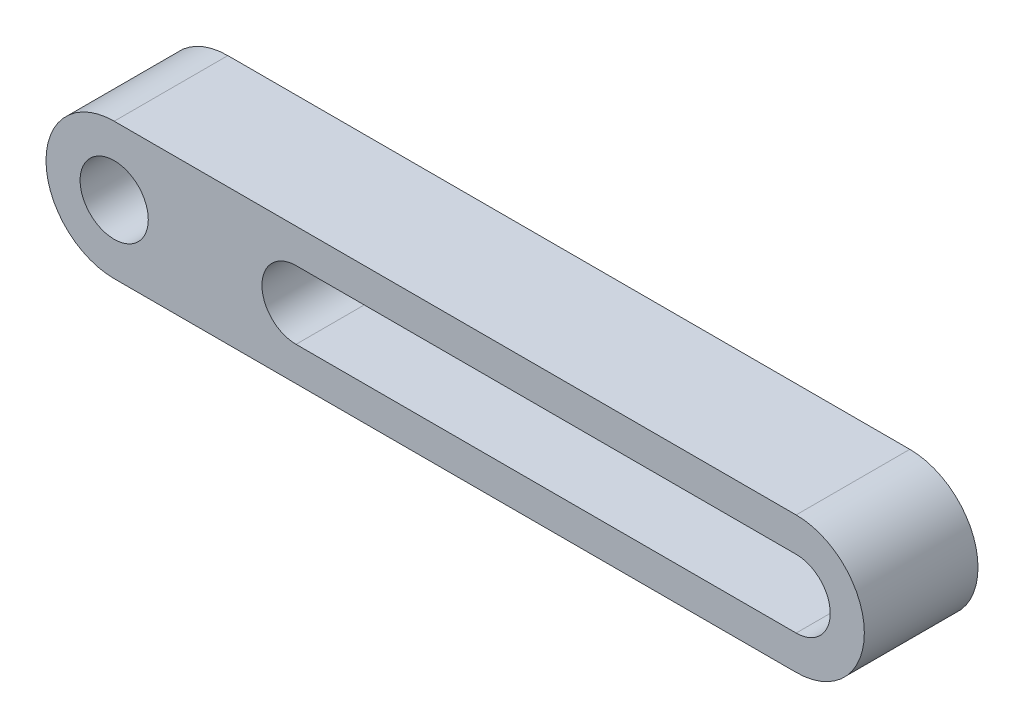
SolidWorks part; units mm, degrees
ref_plane "Front Plane" through (0, 0, 0) normal (0, 0, 1) x (1, 0, 0)
ref_plane "Top Plane" through (0, 0, 0) normal (0, 1, 0) x (1, 0, 0)
ref_plane "Right Plane" through (0, 0, 0) normal (1, 0, 0) x (0, 0, -1)
sketch "Sketch1" plane through (0, 0, 0) normal (0, 0, 1) x (1, 0, 0)
  line L0 (0, 0) -> (30, 0) construction
  line L1 (0, 3) -> (30, 3)
  line L2 (0, -3) -> (30, -3)
  line L3 (30, 0) -> (8, 0) construction
  line L4 (30, -1.5) -> (8, -1.5)
  line L5 (30, 1.5) -> (8, 1.5)
  arc A0 (0, 3) -> (0, -3) centre (0, 0) ccw
  arc A1 (30, -3) -> (30, 3) centre (30, 0) ccw
  circle A3 centre (0, 0) radius 1.5
  arc A4 (30, -1.5) -> (30, 1.5) centre (30, 0) ccw
  arc A5 (8, 1.5) -> (8, -1.5) centre (8, 0) ccw
  point P3 (15, 0)
  point P12 (19, 0)
  dimension "D1" = 3
  dimension "D4" = 3
  dimension "D3" = 1.5
  dimension "D2" = 30
  dimension "Slot Length" = 22
extrude "Boss-Extrude1" add sketch "Sketch1" along normal blind 5
equation "\"D3@Sketch1\"=\"D4@Sketch1\"/2"
